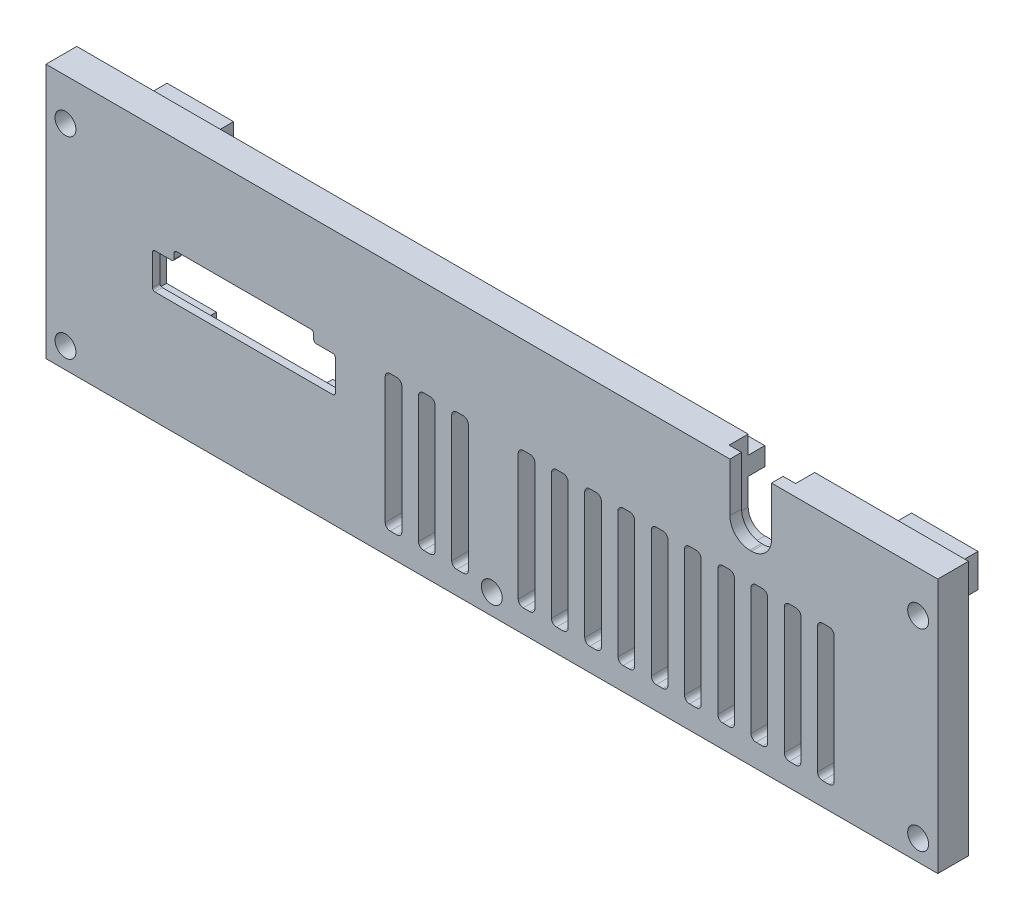
SolidWorks part; units mm, degrees
ref_plane "Front Plane" through (0, 0, 0) normal (0, 0, 1) x (1, 0, 0)
ref_plane "Top Plane" through (0, 0, 0) normal (0, 1, 0) x (1, 0, 0)
ref_plane "Right Plane" through (0, 0, 0) normal (1, 0, 0) x (0, 0, -1)
sketch "Sketch1" plane through (0, 0, 0) normal (0, 0, 1) x (1, 0, 0)
  line L1 (0, 0) -> (136.2202, 0)
  line L2 (0, 0) -> (0, 38.9636)
  line L3 (0, 38.9636) -> (136.2202, 38.9636)
  line L4 (136.2202, 0) -> (136.2202, 38.9636)
  dimension "D1" = 136.2202
  dimension "D2" = 38.9636
extrude "Boss-Extrude1" add sketch "Sketch1" along normal blind 4.699
sketch "Sketch2" plane through (0, 0, 4.699) normal (0, 0, 1) x (1, 0, 0)
  line L0 (16.637, 17.1529) -> (43.815, 17.1529)
  line L1 (44.196, 17.5339) -> (44.196, 22.2329)
  line L2 (43.815, 22.6139) -> (41.275, 22.6139)
  line L3 (40.894, 22.9949) -> (40.894, 23.7569)
  line L4 (40.513, 24.1379) -> (19.939, 24.1379)
  line L6 (19.177, 22.6139) -> (16.637, 22.6139)
  line L7 (16.256, 22.2329) -> (16.256, 17.5339)
  line L8 (19.558, 23.7569) -> (19.558, 22.9949)
  line L9 (0, 19.8834) -> (-19.1232, 19.8834) construction
  line L10 (0, 38.9636) -> (0, 0) construction
  arc A0 (16.637, 22.6139) -> (16.256, 22.2329) centre (16.637, 22.2329) ccw
  arc A1 (16.637, 17.1529) -> (16.256, 17.5339) centre (16.637, 17.5339) cw
  arc A2 (43.815, 17.1529) -> (44.196, 17.5339) centre (43.815, 17.5339) ccw
  arc A3 (44.196, 22.2329) -> (43.815, 22.6139) centre (43.815, 22.2329) ccw
  arc A4 (41.275, 22.6139) -> (40.894, 22.9949) centre (41.275, 22.9949) cw
  arc A5 (40.894, 23.7569) -> (40.513, 24.1379) centre (40.513, 23.7569) ccw
  arc A6 (19.939, 24.1379) -> (19.558, 23.7569) centre (19.939, 23.7569) ccw
  arc A7 (19.558, 22.9949) -> (19.177, 22.6139) centre (19.177, 22.9949) cw
  point P28 (16.256, 19.8834)
  dimension "D6" = 0.381
  dimension "D1" = 5.461
  dimension "D2" = 6.985
  dimension "D3" = 21.336
  dimension "D4" = 27.94
  dimension "D5" = 3.302
  dimension "D7" = 16.256
extrude "Cut-Extrude1" cut sketch "Sketch2" against normal through all
sketch "Sketch3" plane through (0, 0, 0) normal (0, 0, -1) x (-1, 0, 0)
  line L0 (-30.226, 9.9139) -> (-30.226, 2.5732) construction
  line L1 (-11.176, 9.9139) -> (-49.276, 9.9139)
  line L2 (-11.176, 9.9139) -> (-11.176, 31.2499)
  line L3 (-11.176, 31.2499) -> (-49.276, 31.2499)
  line L4 (-49.276, 9.9139) -> (-49.276, 31.2499)
  line L5 (-30.226, 17.1529) -> (-30.226, 22.8158) construction
  line L6 (-16.637, 17.1529) -> (-43.815, 17.1529) construction
  dimension "D1" = 21.336
  dimension "D2" = 38.1
  dimension "D3" = 7.239
extrude "Cut-Extrude3" cut sketch "Sketch3" against normal offset from surface (3.556 mm away) 1.143 up to face at (30.226, 21.6297, 4.699)
hole_wizard "M3 Clearance Hole1" positions "Sketch4" profile "Sketch5" hole size "M3" standard "ANSI Metric"
sketch "Sketch4" plane through (0, 0, 4.699) normal (0, 0, 1) x (1, 0, 0)
  point P0 (2.9718, 32.6136)
  point P2 (2.9718, 3.175)
  point P4 (68.0974, 3.175)
  point P6 (133.223, 32.6136)
  point P8 (133.223, 3.175)
sketch "Sketch5" plane through (2.9718, 32.6136, 4.699) normal (1, 0, 0) x (0, -1, 0)
  line L0 (0, 0) -> (0, 4.826)
  line L1 (0, 4.826) -> (1.6, 4.826)
  line L2 (1.6, 4.826) -> (1.6, 0)
  line L5 (1.6, 0) -> (0, 0)
  line L10 (0, 4.826) -> (-1.6, 4.826) construction
  line L11 (0, -6.35) -> (0, 107.95) construction
  dimension "Hole Dia." = 3.2
  dimension "Hole Depth" = 4.826
  dimension "Drill Angle" = 180
sketch "Sketch6" plane through (0, 0, 0) normal (0, 0, -1) x (-1, 0, 0)
  line L0 (-130.048, 36.1696) -> (-130.048, 0) construction
  line L1 (-130.048, 33.3756) -> (-119.888, 33.3756)
  line L2 (-130.048, 33.3756) -> (-130.048, 28.2956)
  line L10 (-136.2202, 38.9636) -> (0, 38.9636) construction
  line L11 (-119.888, 33.3756) -> (-119.888, 28.2956)
  line L12 (-119.888, 28.2956) -> (-130.048, 28.2956)
  line L13 (-68.1101, 38.9636) -> (-68.1101, -12.8881) construction
  line L22 (-16.3322, 28.2956) -> (-6.1722, 28.2956)
  line L23 (-16.3322, 33.3756) -> (-16.3322, 28.2956)
  line L24 (-6.1722, 33.3756) -> (-6.1722, 28.2956)
  line L25 (-6.1722, 33.3756) -> (-16.3322, 33.3756)
  dimension "D1" = 5.588
  dimension "D2" = 5.08
  dimension "D3" = 10.16
extrude "Boss-Extrude3" add sketch "Sketch6" along normal blind 7.62 and the other way up to surface (4.699 mm away)
sketch "Sketch7" plane through (0, 0, 0) normal (0, 0, -1) x (-1, 0, 0)
  line L0 (-136.2202, 38.9636) -> (0, 38.9636) construction
  line L1 (-122.682, 36.1696) -> (-13.5382, 36.1696)
  line L2 (-122.682, 36.1696) -> (-122.682, 33.3756)
  line L3 (-122.682, 33.3756) -> (-13.5382, 33.3756)
  line L4 (-13.5382, 36.1696) -> (-13.5382, 33.3756)
  line L5 (-130.048, 33.3756) -> (-130.048, 28.2956) construction
  line L6 (-6.1722, 28.2956) -> (-6.1722, 33.3756) construction
  line L7 (-119.888, 33.3756) -> (-130.048, 33.3756) construction
  dimension "D1" = 2.794
  dimension "D3" = 7.366
  dimension "D4" = 7.366
extrude "Boss-Extrude4" add sketch "Sketch7" along normal blind 2.54
fillet "Fillet1" radius 2.54 2 edges at (14.9352, 33.3756, -2.54) (121.285, 33.3756, -2.54)
hole_wizard "Tap Drill for M3x0.5 Tap1" positions "Sketch8" profile "Sketch9" hole size "M3x0.5" standard "ANSI Metric" end condition up to next
sketch "Sketch8" plane through (0, 33.3756, 0) normal (0, 1, 0) x (1, 0, 0)
  line L0 (130.048, 3.81) -> (122.682, 3.81) construction
  line L1 (130.048, 0) -> (130.048, 7.62) construction
  line L2 (122.682, 2.54) -> (122.682, 5.08) construction
  line L4 (6.1722, 3.81) -> (13.5382, 3.81) construction
  line L5 (6.1722, 0) -> (6.1722, 7.62) construction
  line L6 (13.5382, 5.08) -> (13.5382, 2.54) construction
  point P0 (126.365, 3.81)
  point P2 (9.8552, 3.81)
  point P13 (126.365, 3.81)
  point P22 (9.8552, 3.81)
sketch "Sketch9" plane through (126.365, 33.3756, -3.81) normal (1, 0, 0) x (0, 0, 1)
  line L0 (0, 0) -> (0, 5.08)
  line L1 (0, 5.08) -> (1.25, 5.08)
  line L2 (1.25, 5.08) -> (1.25, 0)
  line L5 (1.25, 0) -> (0, 0)
  line L11 (0, -6.35) -> (0, 107.95) construction
  dimension "Thru Hole Dia." = 2.5
  dimension "Thru Hole Depth" = 5.08
sketch "Sketch10" plane through (0, 0, 4.699) normal (0, 0, 1) x (1, 0, 0)
  line L0 (136.2202, 38.9636) -> (0, 38.9636) construction
  line L1 (104.4702, 38.9636) -> (110.8202, 38.9636)
  line L2 (104.4702, 38.9636) -> (104.4702, 31.4706)
  line L3 (107.5182, 28.4226) -> (107.7722, 28.4226)
  line L4 (110.8202, 38.9636) -> (110.8202, 31.4706)
  line L5 (136.2202, 0) -> (136.2202, 38.9636) construction
  arc A0 (107.7722, 28.4226) -> (110.8202, 31.4706) centre (107.7722, 31.4706) ccw
  arc A1 (104.4702, 31.4706) -> (107.5182, 28.4226) centre (107.5182, 31.4706) ccw
  point P10 (110.8202, 28.4226)
  point P13 (104.4702, 28.4226)
  dimension "D4" = 3.048
  dimension "D1" = 6.35
  dimension "D2" = 25.4
  dimension "D3" = 10.541
extrude "Cut-Extrude4" cut sketch "Sketch10" against normal through all
sketch "Sketch11" plane through (0, 0, -2.54) normal (0, 0, -1) x (-1, 0, 0)
  line L0 (-104.4702, 38.9636) -> (0, 38.9636) construction
  line L1 (-110.1852, 26.7716) -> (-105.1052, 26.7716)
  line L2 (-112.7252, 29.3116) -> (-112.7252, 38.9636)
  line L3 (-112.7252, 38.9636) -> (-102.5652, 38.9636)
  line L4 (-102.5652, 29.3116) -> (-102.5652, 38.9636)
  line L5 (-107.6452, 28.4226) -> (-107.6452, 48.2475) construction
  line L6 (-107.7722, 28.4226) -> (-107.5182, 28.4226) construction
  line L7 (-136.2202, 38.9636) -> (-110.8202, 38.9636) construction
  arc A0 (-105.1052, 26.7716) -> (-102.5652, 29.3116) centre (-105.1052, 29.3116) ccw
  arc A1 (-110.1852, 26.7716) -> (-112.7252, 29.3116) centre (-110.1852, 29.3116) cw
  point P10 (-107.6452, 26.7716)
  point P13 (-102.5652, 26.7716)
  point P16 (-112.7252, 26.7716)
  dimension "D2" = 2.54
  dimension "D1" = 10.16
  dimension "D3" = 12.192
extrude "Cut-Extrude5" cut sketch "Sketch11" against normal offset from surface (5.461 mm away) 1.778 up to face at (4.5718, 32.6136, 4.699)
sketch "Sketch12" plane through (0, 0, 0) normal (0, 0, 1) x (1, 0, 0)
  line L0 (0, 0) -> (136.2202, 0) construction
  line L5 (30.226, 17.1529) -> (30.226, 0) construction
  line L6 (16.637, 17.1529) -> (43.815, 17.1529) construction
  line L7 (30.226, 8.5765) -> (-7.3155, 8.5765) construction
  line L29 (52.578, 24.3245) -> (53.594, 24.3245)
  line L34 (51.816, 23.5625) -> (51.816, 4.2585)
  line L35 (52.578, 3.4965) -> (53.594, 3.4965)
  line L36 (54.356, 23.5625) -> (54.356, 4.2585)
  line L37 (57.658, 24.3245) -> (58.674, 24.3245)
  line L38 (56.896, 23.5625) -> (56.896, 4.2585)
  line L39 (57.658, 3.4965) -> (58.674, 3.4965)
  line L40 (59.436, 23.5625) -> (59.436, 4.2585)
  line L41 (62.738, 24.3245) -> (63.754, 24.3245)
  line L42 (61.976, 23.5625) -> (61.976, 4.2585)
  line L43 (62.738, 3.4965) -> (63.754, 3.4965)
  line L44 (64.516, 23.5625) -> (64.516, 4.2585)
  line L49 (72.898, 24.3245) -> (73.914, 24.3245)
  line L50 (72.136, 23.5625) -> (72.136, 4.2585)
  line L51 (72.898, 3.4965) -> (73.914, 3.4965)
  line L52 (74.676, 23.5625) -> (74.676, 4.2585)
  line L53 (77.978, 24.3245) -> (78.994, 24.3245)
  line L54 (77.216, 23.5625) -> (77.216, 4.2585)
  line L55 (77.978, 3.4965) -> (78.994, 3.4965)
  line L56 (79.756, 23.5625) -> (79.756, 4.2585)
  line L57 (83.058, 24.3245) -> (84.074, 24.3245)
  line L58 (82.296, 23.5625) -> (82.296, 4.2585)
  line L59 (83.058, 3.4965) -> (84.074, 3.4965)
  line L60 (84.836, 23.5625) -> (84.836, 4.2585)
  line L61 (88.138, 24.3245) -> (89.154, 24.3245)
  line L62 (87.376, 23.5625) -> (87.376, 4.2585)
  line L63 (88.138, 3.4965) -> (89.154, 3.4965)
  line L64 (89.916, 23.5625) -> (89.916, 4.2585)
  line L65 (93.218, 24.3245) -> (94.234, 24.3245)
  line L66 (92.456, 23.5625) -> (92.456, 4.2585)
  line L67 (93.218, 3.4965) -> (94.234, 3.4965)
  line L68 (94.996, 23.5625) -> (94.996, 4.2585)
  line L69 (98.298, 24.3245) -> (99.314, 24.3245)
  line L70 (97.536, 23.5625) -> (97.536, 4.2585)
  line L71 (98.298, 3.4965) -> (99.314, 3.4965)
  line L72 (100.076, 23.5625) -> (100.076, 4.2585)
  line L73 (103.378, 24.3245) -> (104.394, 24.3245)
  line L74 (102.616, 23.5625) -> (102.616, 4.2585)
  line L75 (103.378, 3.4965) -> (104.394, 3.4965)
  line L76 (105.156, 23.5625) -> (105.156, 4.2585)
  line L77 (108.458, 24.3245) -> (109.474, 24.3245)
  line L78 (107.696, 23.5625) -> (107.696, 4.2585)
  line L79 (108.458, 3.4965) -> (109.474, 3.4965)
  line L80 (110.236, 23.5625) -> (110.236, 4.2585)
  line L81 (113.538, 24.3245) -> (114.554, 24.3245)
  line L82 (112.776, 23.5625) -> (112.776, 4.2585)
  line L83 (113.538, 3.4965) -> (114.554, 3.4965)
  line L84 (115.316, 23.5625) -> (115.316, 4.2585)
  line L85 (118.618, 24.3245) -> (119.634, 24.3245)
  line L86 (117.856, 23.5625) -> (117.856, 4.2585)
  line L87 (118.618, 3.4965) -> (119.634, 3.4965)
  line L88 (120.396, 23.5625) -> (120.396, 4.2585)
  arc A28 (51.816, 4.2585) -> (52.578, 3.4965) centre (52.578, 4.2585) ccw
  arc A29 (53.594, 3.4965) -> (54.356, 4.2585) centre (53.594, 4.2585) ccw
  arc A30 (53.594, 24.3245) -> (54.356, 23.5625) centre (53.594, 23.5625) cw
  arc A31 (52.578, 24.3245) -> (51.816, 23.5625) centre (52.578, 23.5625) ccw
  arc A32 (56.896, 4.2585) -> (57.658, 3.4965) centre (57.658, 4.2585) ccw
  arc A33 (58.674, 3.4965) -> (59.436, 4.2585) centre (58.674, 4.2585) ccw
  arc A34 (58.674, 24.3245) -> (59.436, 23.5625) centre (58.674, 23.5625) cw
  arc A35 (57.658, 24.3245) -> (56.896, 23.5625) centre (57.658, 23.5625) ccw
  arc A36 (61.976, 4.2585) -> (62.738, 3.4965) centre (62.738, 4.2585) ccw
  arc A37 (63.754, 3.4965) -> (64.516, 4.2585) centre (63.754, 4.2585) ccw
  arc A38 (63.754, 24.3245) -> (64.516, 23.5625) centre (63.754, 23.5625) cw
  arc A39 (62.738, 24.3245) -> (61.976, 23.5625) centre (62.738, 23.5625) ccw
  arc A44 (72.136, 4.2585) -> (72.898, 3.4965) centre (72.898, 4.2585) ccw
  arc A45 (73.914, 3.4965) -> (74.676, 4.2585) centre (73.914, 4.2585) ccw
  arc A46 (73.914, 24.3245) -> (74.676, 23.5625) centre (73.914, 23.5625) cw
  arc A47 (72.898, 24.3245) -> (72.136, 23.5625) centre (72.898, 23.5625) ccw
  arc A48 (77.216, 4.2585) -> (77.978, 3.4965) centre (77.978, 4.2585) ccw
  arc A49 (78.994, 3.4965) -> (79.756, 4.2585) centre (78.994, 4.2585) ccw
  arc A50 (78.994, 24.3245) -> (79.756, 23.5625) centre (78.994, 23.5625) cw
  arc A51 (77.978, 24.3245) -> (77.216, 23.5625) centre (77.978, 23.5625) ccw
  arc A52 (82.296, 4.2585) -> (83.058, 3.4965) centre (83.058, 4.2585) ccw
  arc A53 (84.074, 3.4965) -> (84.836, 4.2585) centre (84.074, 4.2585) ccw
  arc A54 (84.074, 24.3245) -> (84.836, 23.5625) centre (84.074, 23.5625) cw
  arc A55 (83.058, 24.3245) -> (82.296, 23.5625) centre (83.058, 23.5625) ccw
  arc A56 (87.376, 4.2585) -> (88.138, 3.4965) centre (88.138, 4.2585) ccw
  arc A57 (89.154, 3.4965) -> (89.916, 4.2585) centre (89.154, 4.2585) ccw
  arc A58 (89.154, 24.3245) -> (89.916, 23.5625) centre (89.154, 23.5625) cw
  arc A59 (88.138, 24.3245) -> (87.376, 23.5625) centre (88.138, 23.5625) ccw
  arc A60 (92.456, 4.2585) -> (93.218, 3.4965) centre (93.218, 4.2585) ccw
  arc A61 (94.234, 3.4965) -> (94.996, 4.2585) centre (94.234, 4.2585) ccw
  arc A62 (94.234, 24.3245) -> (94.996, 23.5625) centre (94.234, 23.5625) cw
  arc A63 (93.218, 24.3245) -> (92.456, 23.5625) centre (93.218, 23.5625) ccw
  arc A64 (97.536, 4.2585) -> (98.298, 3.4965) centre (98.298, 4.2585) ccw
  arc A65 (99.314, 3.4965) -> (100.076, 4.2585) centre (99.314, 4.2585) ccw
  arc A66 (99.314, 24.3245) -> (100.076, 23.5625) centre (99.314, 23.5625) cw
  arc A67 (98.298, 24.3245) -> (97.536, 23.5625) centre (98.298, 23.5625) ccw
  arc A68 (102.616, 4.2585) -> (103.378, 3.4965) centre (103.378, 4.2585) ccw
  arc A69 (104.394, 3.4965) -> (105.156, 4.2585) centre (104.394, 4.2585) ccw
  arc A70 (104.394, 24.3245) -> (105.156, 23.5625) centre (104.394, 23.5625) cw
  arc A71 (103.378, 24.3245) -> (102.616, 23.5625) centre (103.378, 23.5625) ccw
  arc A72 (107.696, 4.2585) -> (108.458, 3.4965) centre (108.458, 4.2585) ccw
  arc A73 (109.474, 3.4965) -> (110.236, 4.2585) centre (109.474, 4.2585) ccw
  arc A74 (109.474, 24.3245) -> (110.236, 23.5625) centre (109.474, 23.5625) cw
  arc A75 (108.458, 24.3245) -> (107.696, 23.5625) centre (108.458, 23.5625) ccw
  arc A76 (112.776, 4.2585) -> (113.538, 3.4965) centre (113.538, 4.2585) ccw
  arc A77 (114.554, 3.4965) -> (115.316, 4.2585) centre (114.554, 4.2585) ccw
  arc A78 (114.554, 24.3245) -> (115.316, 23.5625) centre (114.554, 23.5625) cw
  arc A79 (113.538, 24.3245) -> (112.776, 23.5625) centre (113.538, 23.5625) ccw
  arc A80 (117.856, 4.2585) -> (118.618, 3.4965) centre (118.618, 4.2585) ccw
  arc A81 (119.634, 3.4965) -> (120.396, 4.2585) centre (119.634, 4.2585) ccw
  arc A82 (119.634, 24.3245) -> (120.396, 23.5625) centre (119.634, 23.5625) cw
  arc A83 (118.618, 24.3245) -> (117.856, 23.5625) centre (118.618, 23.5625) ccw
extrude "Cut-Extrude8" cut sketch "Sketch12" along normal through all
sketch "Sketch13" plane through (0, 0, 3.556) normal (0, 0, -1) x (-1, 0, 0)
  line L0 (-39.116, 26.6779) -> (-39.116, 30.3609)
  line L1 (-39.116, 26.6779) -> (-46.736, 26.6779)
  line L3 (-46.736, 26.6779) -> (-46.736, 14.4859)
  line L5 (-46.736, 14.4859) -> (-39.116, 14.4859)
  line L6 (-39.116, 14.4859) -> (-39.116, 10.8029)
  line L10 (-30.226, 17.1529) -> (-30.226, 43.4392) construction
  line L11 (-16.637, 17.1529) -> (-43.815, 17.1529) construction
  line L12 (-39.116, 30.3609) -> (-21.336, 30.3609)
  line L15 (-11.176, 31.2499) -> (-49.276, 31.2499)
  line L16 (-49.276, 31.2499) -> (-49.276, 9.9139)
  line L17 (-39.116, 10.8029) -> (-21.336, 10.8029)
  line L18 (-11.176, 9.9139) -> (-49.276, 9.9139)
  line L21 (-11.176, 31.2499) -> (-11.176, 9.9139)
  line L22 (-21.336, 14.4859) -> (-21.336, 10.8029)
  line L23 (-13.716, 14.4859) -> (-21.336, 14.4859)
  line L24 (-13.716, 26.6779) -> (-13.716, 14.4859)
  line L25 (-21.336, 26.6779) -> (-13.716, 26.6779)
  line L26 (-21.336, 26.6779) -> (-21.336, 30.3609)
  point P19 (-38.9595, 10.8029)
  point P25 (0, 0)
  point P33 (0, 0)
  dimension "D1" = 0.889
  dimension "D2" = 0.889
  dimension "D3" = 10.16
  dimension "D4" = 2.54
  dimension "D5" = 4.572
  dimension "D6" = 4.572
extrude "Boss-Extrude5" add sketch "Sketch13" along normal up to surface (3.556 mm away) up to face at (76.2373, 29.1387, 0)
